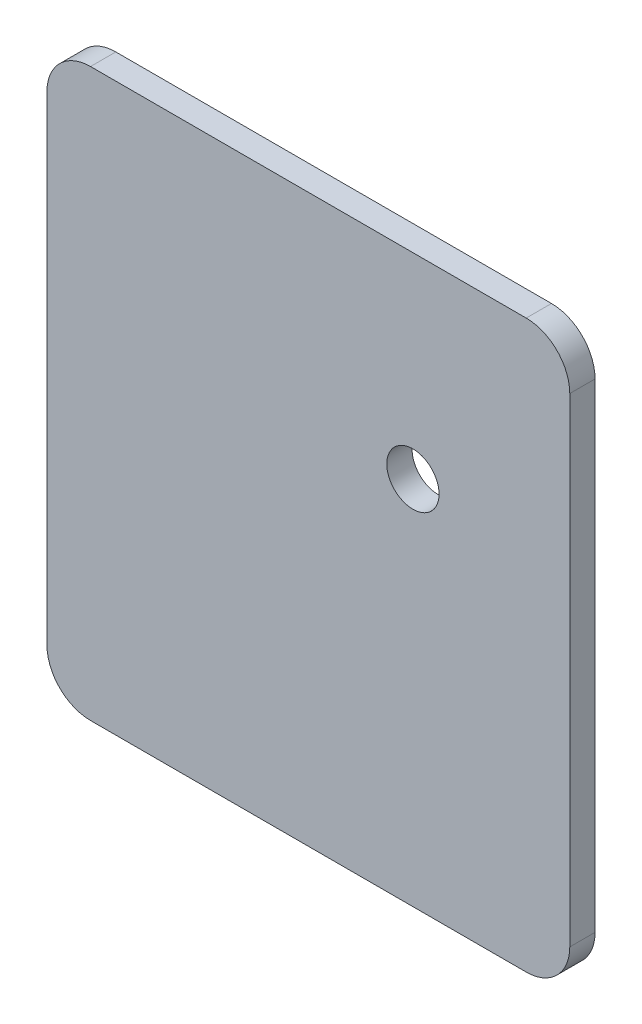
SolidWorks part; units mm, degrees
material "1023 Chapa de acero al carbono (SS)"
ref_plane "Alzado" through (0, 0, 0) normal (0, 0, 1) x (1, 0, 0)
ref_plane "Planta" through (0, 0, 0) normal (0, 1, 0) x (1, 0, 0)
ref_plane "Vista lateral" through (0, 0, 0) normal (1, 0, 0) x (0, 0, -1)
sketch "Croquis1" plane through (0, 0, 0) normal (0, 0, 1) x (1, 0, 0)
  line L0 (0, 0) -> (0, 65)
  line L1 (0, 65) -> (60, 65)
  line L2 (0, 0) -> (60, 0)
  line L3 (60, 0) -> (60, 65)
  circle A0 centre (42, 42.5) radius 3
  dimension "D3" = 6
  dimension "D1" = 60
  dimension "D2" = 65
  dimension "D4" = 42.5
  dimension "D5" = 18
extrude "Saliente-Extruir1" add sketch "Croquis1" against normal blind 2.9
fillet "Redondeo2" radius 5 1 edges at (0, 65, -1.45)
fillet "Redondeo3" radius 5 1 edges at (60, 65, -1.45)
fillet "Redondeo4" radius 5 1 edges at (60, 0, -1.45)
fillet "Redondeo5" radius 5 1 edges at (0, 0, -1.45)
